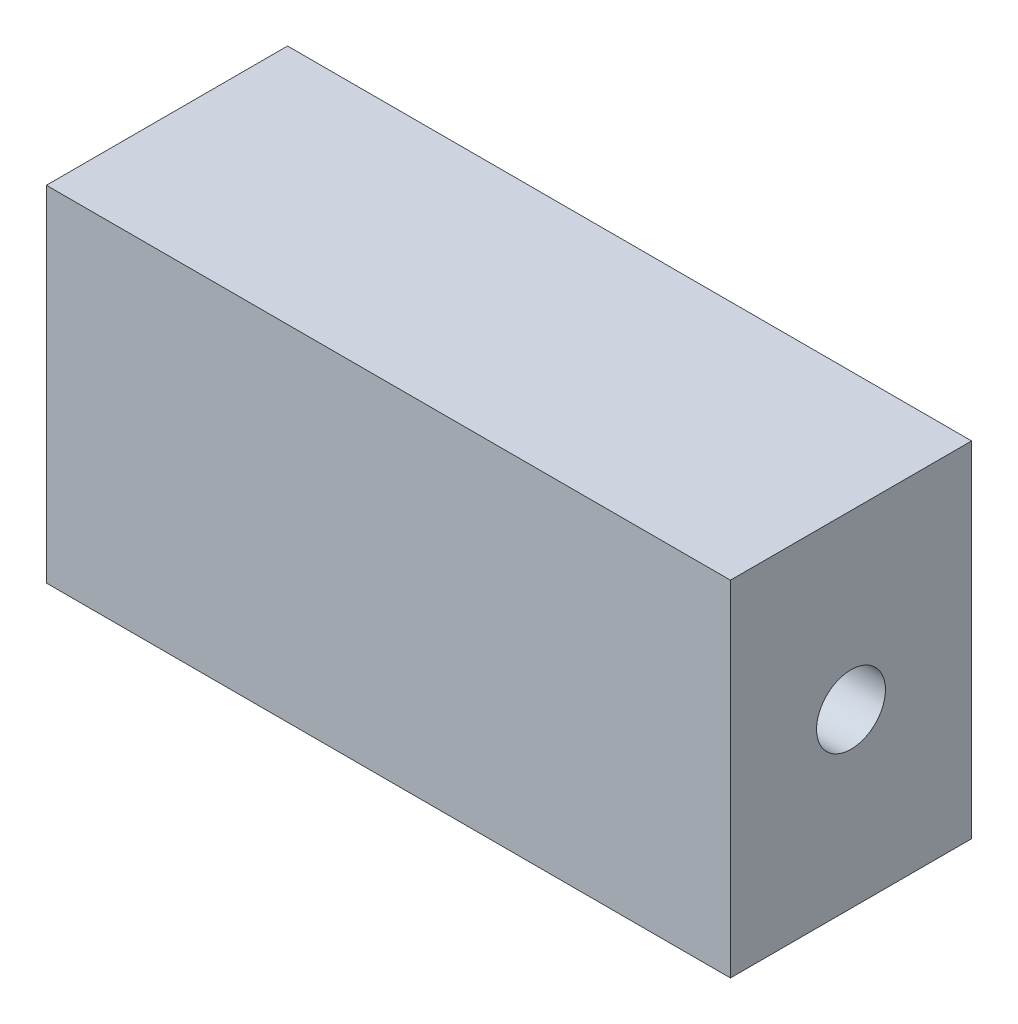
SolidWorks part; units mm, degrees
ref_plane "Front Plane" through (0, 0, 0) normal (0, 0, 1) x (1, 0, 0)
ref_plane "Top Plane" through (0, 0, 0) normal (0, 1, 0) x (1, 0, 0)
ref_plane "Right Plane" through (0, 0, 0) normal (1, 0, 0) x (0, 0, -1)
sketch "Sketch1" plane through (0, 0, 0) normal (0, 1, 0) x (1, 0, 0)
  line L1 (-49.635, -17.5) -> (49.635, -17.5)
  line L2 (-49.635, -17.5) -> (-49.635, 17.5)
  line L3 (-49.635, 17.5) -> (49.635, 17.5)
  line L4 (49.635, -17.5) -> (49.635, 17.5)
  line L5 (-49.635, -17.5) -> (49.635, 17.5) construction
  line L6 (-49.635, 17.5) -> (49.635, -17.5) construction
  point P0 (0, 0)
extrude "Boss-Extrude1" add sketch "Sketch1" along normal blind 50
sketch "Sketch2" plane through (-49.635, 0, 0) normal (-1, 0, 0) x (0, 0, 1)
  line L0 (-17.5, 50) -> (17.5, 0) construction
  line L1 (-17.5, 0) -> (17.5, 50) construction
  circle A0 centre (0, 25) radius 5
extrude "Cut-Extrude1" cut sketch "Sketch2" against normal blind 10
sketch "Sketch3" plane through (49.635, 0, 0) normal (1, 0, 0) x (0, 0, -1)
  line L0 (-17.5, 50) -> (17.5, 0) construction
  line L1 (-17.5, 0) -> (17.5, 50) construction
  circle A0 centre (0, 25) radius 5
extrude "Cut-Extrude2" cut sketch "Sketch3" against normal blind 10
